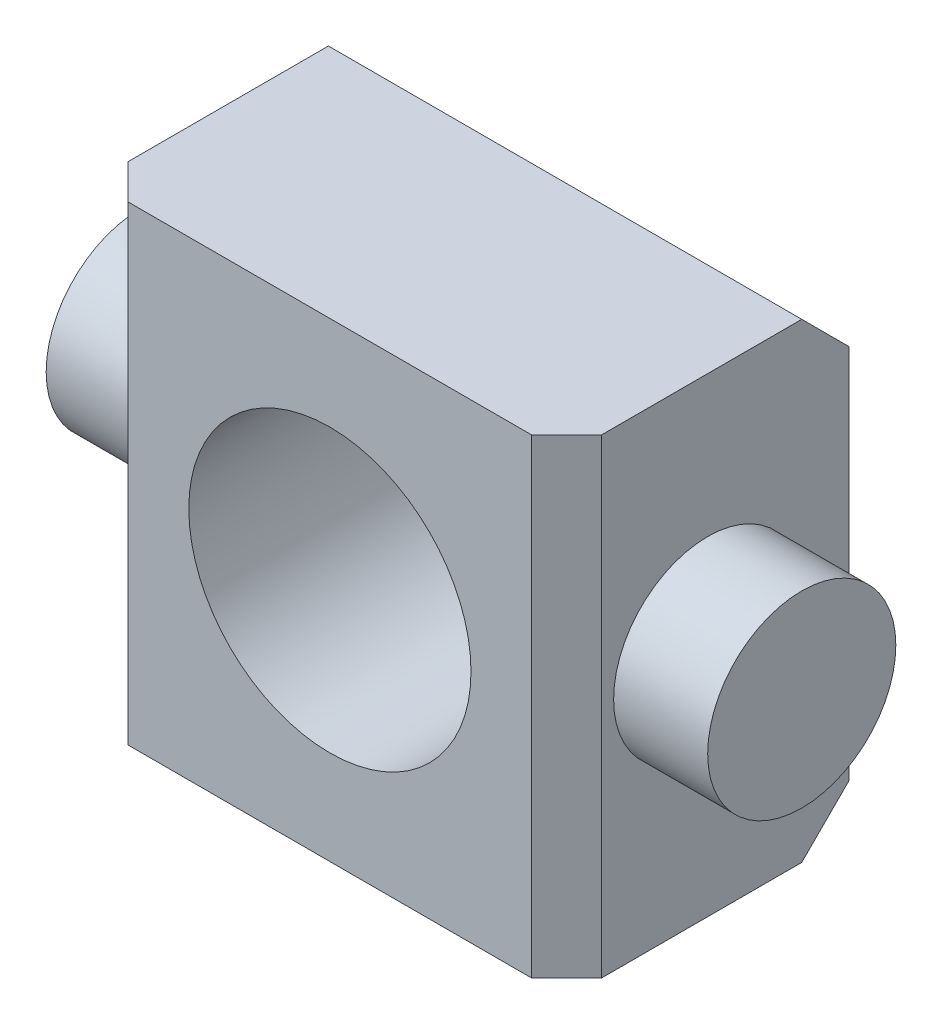
SolidWorks part; units mm, degrees
material "NITRONIC 60"
ref_plane "XY" through (0, 0, 0) normal (0, 0, 1) x (1, 0, 0)
ref_plane "XZ" through (0, 0, 0) normal (0, 1, 0) x (1, 0, 0)
ref_plane "YZ" through (0, 0, 0) normal (1, 0, 0) x (0, 0, -1)
sketch "Sketch1" plane through (0, 0, 0) normal (0, 0, 1) x (1, 0, 0)
  line L0 (15.9766, 15.875) -> (-15.9766, -15.875) construction
  line L1 (-15.9766, 15.875) -> (15.9766, 15.875)
  line L2 (-15.9766, 15.875) -> (-15.9766, -15.875)
  line L3 (-15.9766, -15.875) -> (15.9766, -15.875)
  line L4 (15.9766, 15.875) -> (15.9766, -15.875)
  dimension "D2" = 31.75
  dimension "D3" = 31.9532
extrude "Extrude1" add sketch "Sketch1" along normal mid plane 19.05
sketch "Sketch2" plane through (-15.9766, 0, 0) normal (-1, 0, 0) x (0, 0, 1)
  circle A0 centre (0, 0) radius 6.35
  dimension "D1" = 12.7
extrude "Extrude2" add sketch "Sketch2" along normal blind 6.35
mirror "Mirror1" about plane through (0, 0, 0) normal (1, 0, 0) of "Extrude2"
chamfer "Chamfer1" distance 3.175 angle 45 2 edges at (0, 15.875, -9.525) (0, -15.875, -9.525)
hole_wizard "3/4-10-ACME-2C-RH Tapped Hole1" positions "Sketch6" profile "Sketch7" tap size "3/4-10" standard "Ansi Inch" end condition through all
sketch "Sketch6" plane through (0, 0, 9.525) normal (0, 0, 1) x (1, 0, 0)
  point P0 (0, 0)
sketch "Sketch7" plane through (0, 0, 9.525) normal (1, 0, 0) x (0, -1, 0)
  line L0 (0, 0) -> (0, 19.05)
  line L1 (0, 19.05) -> (9.525, 19.05)
  line L2 (9.525, 19.05) -> (9.525, 0)
  line L5 (9.525, 0) -> (0, 0)
  line L11 (0, -6.35) -> (0, 107.95) construction
  dimension "Thread Major Dia." = 19.05
  dimension "Thru Tap Drill Depth" = 19.05
chamfer "Chamfer2" distance 2.3622 angle 45 2 edges at (15.9766, 0, 9.525) (-15.9766, 0, 9.525)
